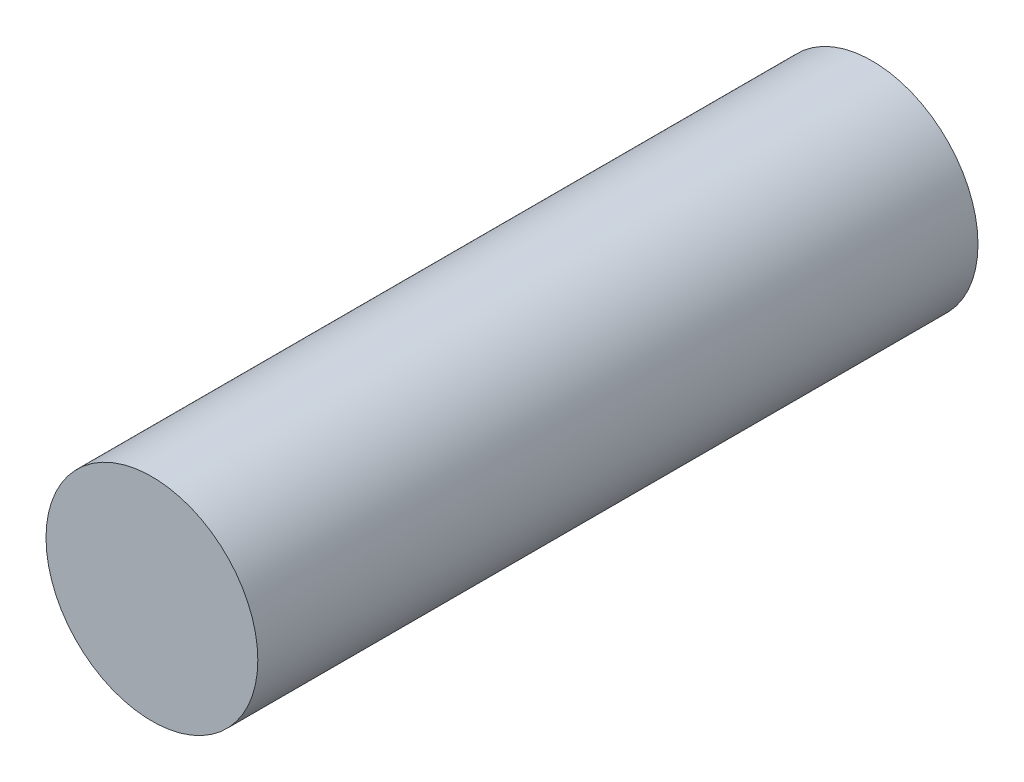
SolidWorks part; units mm, degrees
material "Сплав 2024"
ref_plane "Спереди" through (0, 0, 0) normal (0, 0, 1) x (1, 0, 0)
ref_plane "Сверху" through (0, 0, 0) normal (0, 1, 0) x (1, 0, 0)
ref_plane "Справа" through (0, 0, 0) normal (1, 0, 0) x (0, 0, -1)
sketch "Эскиз1" plane through (0, 0, 0) normal (0, 0, 1) x (1, 0, 0)
  circle A0 centre (0, 0) radius 2.5
  dimension "D1" = 5
extrude "Бобышка-Вытянуть1" add sketch "Эскиз1" along normal blind 17
